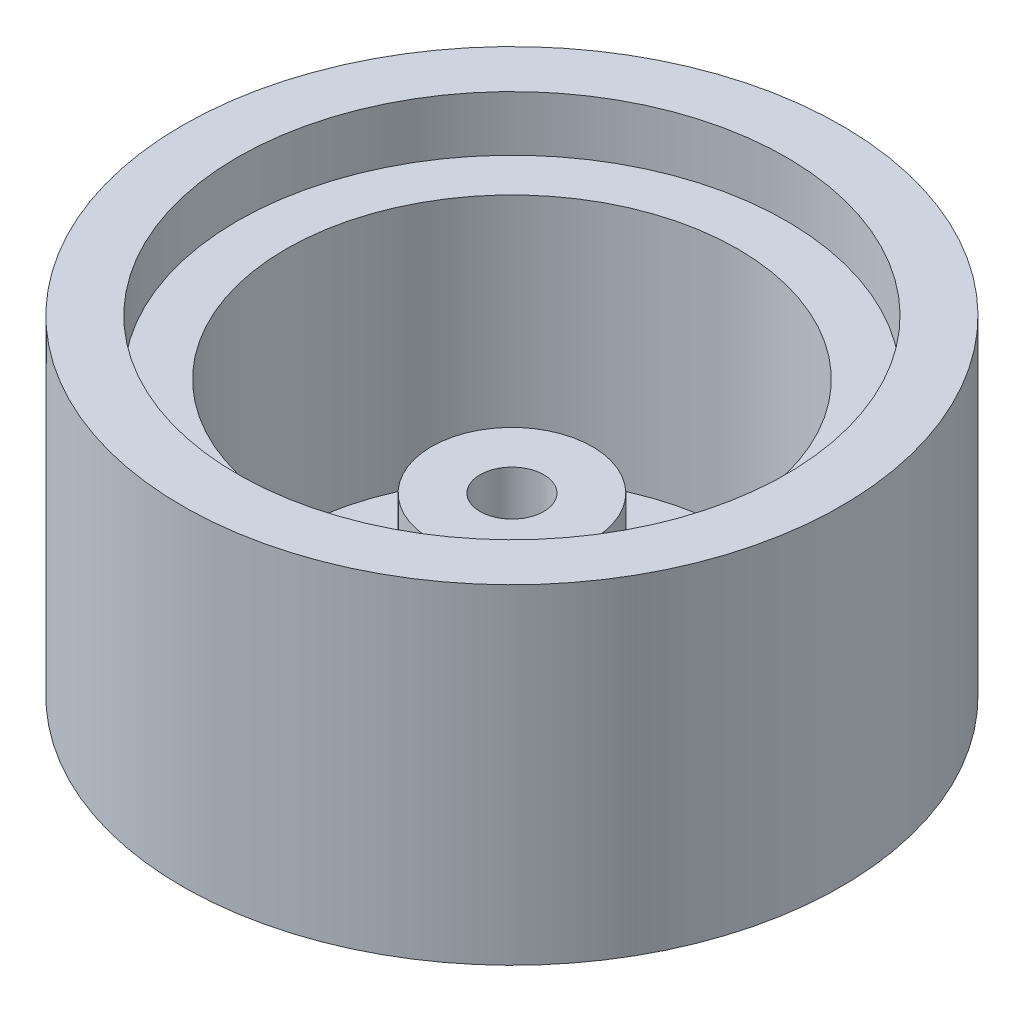
SolidWorks part; units mm, degrees
material "Brass"
ref_plane "Front Plane" through (0, 0, 0) normal (0, 0, 1) x (1, 0, 0)
ref_plane "Top Plane" through (0, 0, 0) normal (0, 1, 0) x (1, 0, 0)
ref_plane "Right Plane" through (0, 0, 0) normal (1, 0, 0) x (0, 0, -1)
other "Center of Mass"
sketch "Sketch1" plane through (0, 0, 0) normal (0, 0, 1) x (1, 0, 0)
  line L0 (20.9, -10.5921) -> (7.45, -10.5921)
  line L1 (0, 55.6945) -> (0, -36.096) construction
  line L2 (2.95, -13.1921) -> (30.5, -13.1921)
  line L3 (30.5, -13.1921) -> (30.5, 17.3079)
  line L4 (30.5, 17.3079) -> (25.4, 17.3079)
  line L5 (25.4, 17.3079) -> (25.4, 12.2079)
  line L6 (25.4, 12.2079) -> (20.9, 12.2079)
  line L7 (20.9, 12.2079) -> (20.9, -10.5921)
  line L8 (7.45, 3.0879) -> (7.45, -10.5921)
  line L9 (7.45, 3.0879) -> (2.95, 3.0879)
  line L10 (2.95, 3.0879) -> (2.95, -13.1921)
revolve "Revolve1" add sketch "Sketch1" angle 360 about L1
